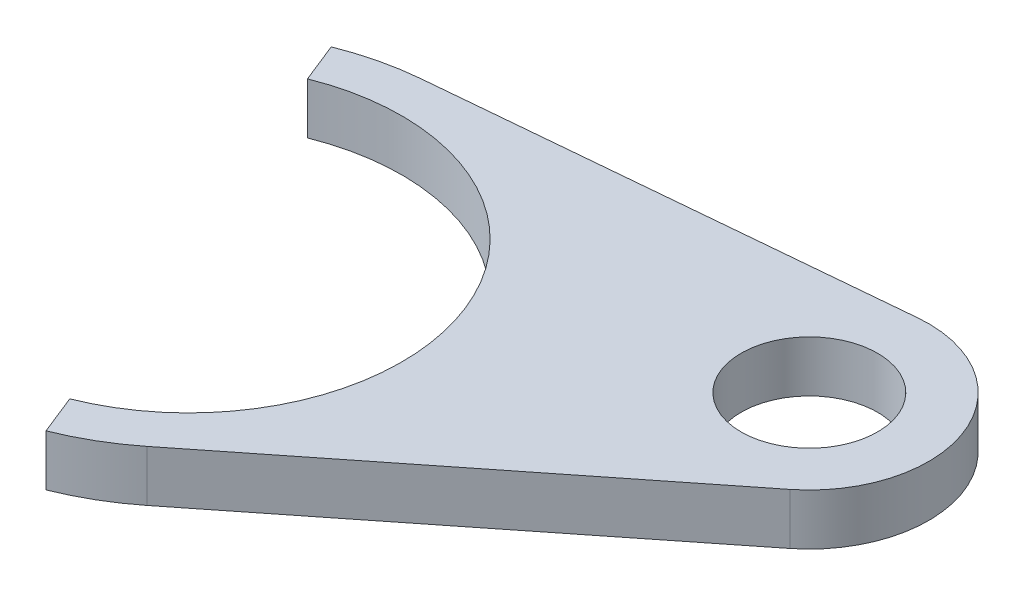
SolidWorks part; units mm, degrees
material "1.0045 (S355JR)"
ref_plane "Płaszczyzna przednia" through (0, 0, 0) normal (0, 0, 1) x (1, 0, 0)
ref_plane "Płaszczyzna górna" through (0, 0, 0) normal (0, 1, 0) x (1, 0, 0)
ref_plane "Płaszczyzna prawa" through (0, 0, 0) normal (1, 0, 0) x (0, 0, -1)
sketch "Szkic1" plane through (0, 0, 0) normal (0, 1, 0) x (1, 0, 0)
  line L0 (-1700.6952, -413.9173) -> (-1679.6631, -397.2544)
  line L1 (-1711.3656, -387.2214) -> (-1684.6426, -384.7963)
  line L2 (-1704.4427, -416.0886) -> (-1705.3706, -413.7671)
  line L3 (-1710.01, -402.16) -> (-1684.01, -391.7677) construction
  line L4 (-1714.6494, -390.5529) -> (-1715.5773, -388.2314)
  arc A0 (-1711.3656, -387.2214) -> (-1715.5773, -388.2314) centre (-1710.01, -402.16) ccw
  arc A1 (-1705.3706, -413.7671) -> (-1714.6494, -390.5529) centre (-1710.01, -402.16) ccw
  arc A2 (-1679.6631, -397.2544) -> (-1684.6426, -384.7963) centre (-1684.01, -391.7677) ccw
  circle A3 centre (-1684.01, -391.7677) radius 4
  arc A4 (-1704.4427, -416.0886) -> (-1700.6952, -413.9173) centre (-1710.01, -402.16) ccw
  dimension "D1" = 25
  dimension "D2" = 30
  dimension "D3" = 8
  dimension "D4" = 14
  dimension "D5" = 28
  dimension "D6" = 26
  dimension "D7" = 402.16
  dimension "D8" = 1710.01
extrude "Dodanie-wyciągnięcie1" add sketch "Szkic1" along normal blind 3
